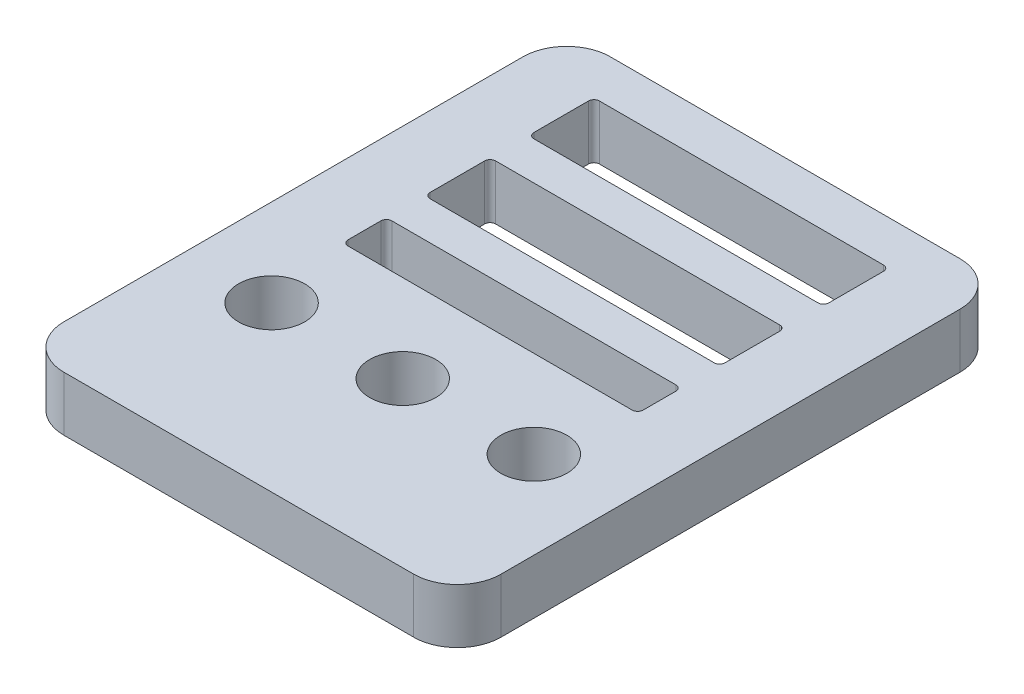
SolidWorks part; units mm, degrees
ref_plane "Front Plane" through (0, 0, 0) normal (0, 0, 1) x (1, 0, 0)
ref_plane "Top Plane" through (0, 0, 0) normal (0, 1, 0) x (1, 0, 0)
ref_plane "Right Plane" through (0, 0, 0) normal (1, 0, 0) x (0, 0, -1)
sketch "Sketch1" plane through (0, 0, 0) normal (0, 1, 0) x (1, 0, 0)
  line L1 (-20, -25) -> (20, -25)
  line L2 (-20, -25) -> (-20, 25)
  line L3 (-20, 25) -> (20, 25)
  line L4 (20, -25) -> (20, 25)
  line L5 (0, 25) -> (0, -25) construction
  line L6 (-20, 0) -> (20, 0) construction
  point P0 (0, 0)
  dimension "D1" = 40
  dimension "D2" = 50
extrude "Boss-Extrude1" add sketch "Sketch1" along normal blind 5
sketch "Sketch2" plane through (0, 5, 0) normal (0, 1, 0) x (1, 0, 0)
  line L0 (0, 25) -> (0, -25) construction
  line L1 (20, 25) -> (-20, 25) construction
  line L2 (-20, -25) -> (20, -25) construction
  line L4 (-13.5, 21) -> (13.5, 21)
  line L5 (-13.5, 21) -> (-13.5, 15)
  line L6 (-13.5, 15) -> (13.5, 15)
  line L7 (13.5, 21) -> (13.5, 15)
  line L8 (0, 15) -> (0, 21) construction
  line L9 (-13.5, 18) -> (13.5, 18) construction
  line L10 (-13.5, 11.5) -> (13.5, 11.5)
  line L11 (-13.5, 11.5) -> (-13.5, 5.5)
  line L12 (-13.5, 5.5) -> (13.5, 5.5)
  line L13 (13.5, 11.5) -> (13.5, 5.5)
  line L14 (0, 5.5) -> (0, 11.5) construction
  line L15 (-13.5, 8.5) -> (13.5, 8.5) construction
  line L16 (-13.5, 2) -> (13.5, 2)
  line L17 (-13.5, 2) -> (-13.5, -2)
  line L18 (-13.5, -2) -> (13.5, -2)
  line L19 (13.5, 2) -> (13.5, -2)
  line L20 (0, -2) -> (0, 2) construction
  line L21 (-13.5, 0) -> (13.5, 0) construction
  point P6 (0, 18)
  point P10 (0, 8.5)
  point P14 (0, 0)
  dimension "D1" = 27
  dimension "D2" = 6
  dimension "D3" = 3.5
  dimension "D4" = 3.5
  dimension "D5" = 4
  dimension "D6" = 4
extrude "Cut-Extrude1" cut sketch "Sketch2" against normal through all
sketch "Sketch3" plane through (0, 5, 0) normal (0, 1, 0) x (1, 0, 0)
  line L0 (-20, -10) -> (20, -10) construction
  line L1 (-20, 25) -> (-20, -25) construction
  line L2 (20, -25) -> (20, 25) construction
  line L3 (-20, -25) -> (20, -25) construction
  circle A0 centre (0, -10) radius 3.025
  dimension "D1" = 6.05
  dimension "D2" = 15
extrude "Cut-Extrude2" cut sketch "Sketch3" against normal through all
pattern_linear "LPattern1" count 2 spacing 12 along (1, 0, 0) count 2 spacing 12 along (-1, 0, 0) of "Cut-Extrude2"
fillet "Fillet1" radius 4 4 edges at (20, 2.5, 25) (-20, 2.5, 25) (20, 2.5, -25) (-20, 2.5, -25)
fillet "Fillet2" radius 0.5 12 edges at (13.5, 2.5, -15) (13.5, 2.5, -5.5) (13.5, 2.5, 2) (-13.5, 2.5, 2) (-13.5, 2.5, -5.5) (-13.5, 2.5, -15) (-13.5, 2.5, -21) (-13.5, 2.5, -11.5) (-13.5, 2.5, -2) (13.5, 2.5, -2) (13.5, 2.5, -11.5) (13.5, 2.5, -21)
